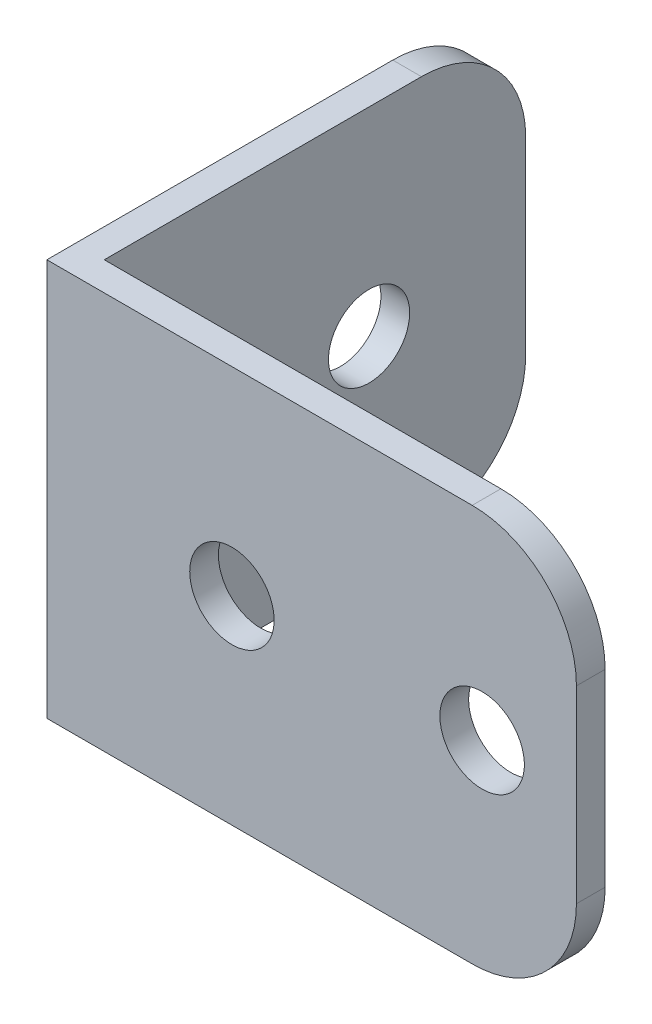
SolidWorks part; units mm, degrees
material "Galvanized Steel"
ref_plane "Front Plane" through (0, 0, 0) normal (0, 0, 1) x (1, 0, 0)
ref_plane "Top Plane" through (0, 0, 0) normal (0, 1, 0) x (1, 0, 0)
ref_plane "Right Plane" through (0, 0, 0) normal (1, 0, 0) x (0, 0, -1)
sketch "Sketch1" plane through (0, 0, 0) normal (0, 1, 0) x (1, 0, 0)
  line L0 (25.4, 21.59) -> (-22.6466, 21.59) construction
  line L1 (-25.4, -21.59) -> (25.4, -21.59)
  line L2 (-25.4, -21.59) -> (-25.4, 21.59)
  line L3 (-25.4, 21.59) -> (-22.6466, 21.59)
  line L4 (25.4, -21.59) -> (25.4, -18.8366)
  line L5 (-25.4, -21.59) -> (25.4, 21.59) construction
  line L6 (-25.4, 21.59) -> (25.4, -21.59) construction
  line L9 (25.4, -18.8366) -> (-22.6466, -18.8366)
  line L10 (-22.6466, 21.59) -> (-22.6466, -18.8366)
  line L15 (25.4, -18.8366) -> (25.4, 21.59) construction
  point P0 (0, 0)
  dimension "D1" = 50.8
  dimension "D2" = 2.7534
  dimension "D3" = 43.18
extrude "Boss-Extrude1" add sketch "Sketch1" along normal blind 38.1
fillet "Fillet1" radius 10 4 edges at (25.4, 38.1, 20.2133) (25.4, 0, 20.2133) (-24.0233, 38.1, -21.59) (-24.0233, 0, -21.59)
sketch "Sketch2" plane through (0, 0, 18.8366) normal (0, 0, -1) x (-1, 0, 0)
  line L0 (-25.4, 28.1) -> (-25.4, 10) construction
  line L1 (22.6466, 38.1) -> (22.6466, 0) construction
  circle A0 centre (-16.3534, 19.05) radius 4.05
  circle A1 centre (7.6466, 19.05) radius 4.05
  point P4 (0, 0)
  point P7 (-25.4, 19.05)
  dimension "D3" = 8.1
  dimension "D1" = 15
  dimension "D2" = 24
extrude "Cut-Extrude1" cut sketch "Sketch2" against normal through all
sketch "Sketch3" plane through (-22.6466, 0, 0) normal (1, 0, 0) x (0, 0, -1)
  line L0 (21.59, 28.1) -> (21.59, 10) construction
  line L1 (-18.8366, 38.1) -> (-18.8366, 0) construction
  circle A0 centre (6.5634, 19.05) radius 3.8939
  point P4 (21.59, 19.05)
  dimension "D1" = 25.4
extrude "Cut-Extrude2" cut sketch "Sketch3" against normal through all
